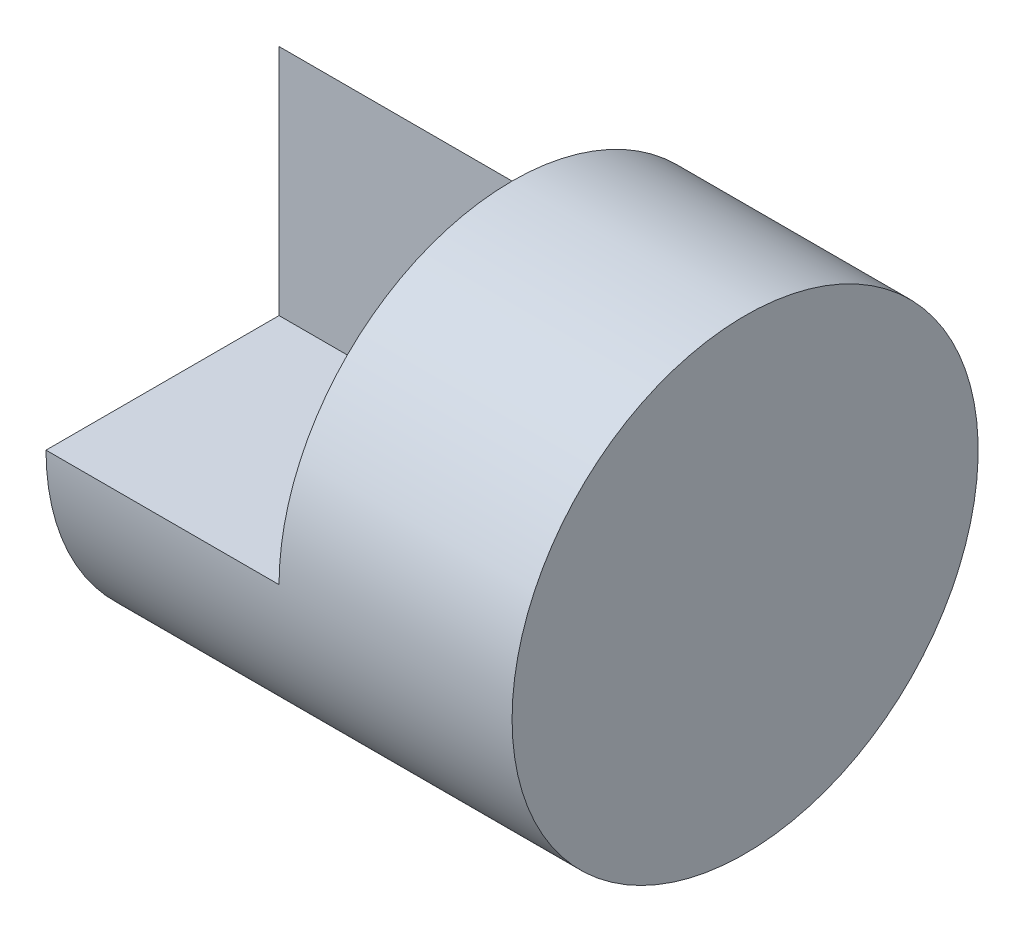
SolidWorks part; units mm, degrees
ref_plane "Front" through (0, 0, 0) normal (0, 0, 1) x (1, 0, 0)
ref_plane "Top" through (0, 0, 0) normal (0, 1, 0) x (1, 0, 0)
ref_plane "Right" through (0, 0, 0) normal (1, 0, 0) x (0, 0, -1)
sketch "Sketch1" plane through (0, 0, 0) normal (0, 1, 0) x (1, 0, 0)
  line L1 (-2, -2) -> (2, -2)
  line L2 (-2, -2) -> (-2, 2)
  line L3 (-2, 2) -> (2, 2)
  line L4 (2, -2) -> (2, 2)
  line L5 (-2, -2) -> (2, 2) construction
  line L6 (-2, 2) -> (2, -2) construction
  point P0 (0, 0)
  dimension "D1" = 4
  dimension "D2" = 4
extrude "Boss-Extrude1" add sketch "Sketch1" along normal blind 4
sketch "Sketch2" plane through (-2, 0, 0) normal (-1, 0, 0) x (0, 0, 1)
  line L0 (-2, 2) -> (0, 4)
  line L3 (0, 4) -> (0, 2)
  line L5 (0, 2) -> (2, 2)
  line L9 (-2, 0) -> (2, 0)
  line L10 (2, 0) -> (2, 4)
  line L11 (2, 4) -> (-2, 4)
  line L12 (-2, 4) -> (-2, 0)
  line L13 (-2, 0) -> (2, 0)
  line L14 (2, 0) -> (2, 4)
  line L15 (2, 4) -> (-2, 4)
  line L16 (-2, 4) -> (-2, 0)
  dimension "D1" = 0
extrude "Cut-Extrude1" cut sketch "Sketch2" against normal blind 2
sketch "Sketch3" plane through (0, 0, 0) normal (-1, 0, 0) x (0, 0, 1)
  circle A0 centre (0, 2) radius 2
  circle A1 centre (0, 2) radius 2.8284
extrude "Cut-Extrude2" cut sketch "Sketch3" against normal mid plane 60
